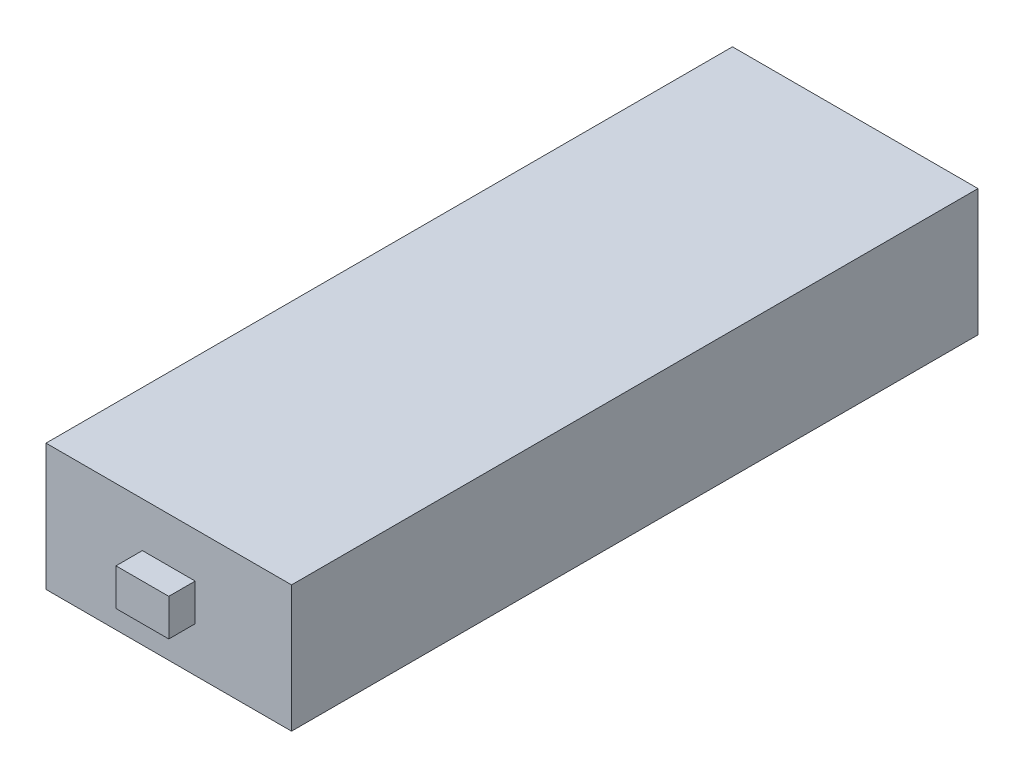
SolidWorks part; units mm, degrees
ref_plane "Front Plane" through (0, 0, 0) normal (0, 0, 1) x (1, 0, 0)
ref_plane "Top Plane" through (0, 0, 0) normal (0, 1, 0) x (1, 0, 0)
ref_plane "Right Plane" through (0, 0, 0) normal (1, 0, 0) x (0, 0, -1)
sketch "Sketch1" plane through (0, 0, 0) normal (0, 1, 0) x (1, 0, 0)
  line L1 (23.25, -65) -> (-23.25, -65)
  line L2 (23.25, -65) -> (23.25, 65)
  line L3 (23.25, 65) -> (-23.25, 65)
  line L4 (-23.25, -65) -> (-23.25, 65)
  line L5 (23.25, -65) -> (-23.25, 65) construction
  line L6 (23.25, 65) -> (-23.25, -65) construction
  point P0 (0, 0)
  dimension "D1" = 46.5
  dimension "D2" = 130
extrude "body" add sketch "Sketch1" along normal blind 24
sketch "Sketch2" plane through (0, 0, 65) normal (0, 0, 1) x (1, 0, 0)
  line L0 (-23.25, 24) -> (-23.25, 0) construction
  line L1 (5, 8.5) -> (-5, 8.5)
  line L2 (5, 8.5) -> (5, 15.5)
  line L3 (5, 15.5) -> (-5, 15.5)
  line L4 (-5, 8.5) -> (-5, 15.5)
  line L5 (5, 8.5) -> (-5, 15.5) construction
  line L6 (5, 15.5) -> (-5, 8.5) construction
  point P0 (0, 12)
  point P5 (0, 0)
  point P9 (-23.25, 12)
  dimension "D1" = 7
  dimension "D2" = 10
extrude "cables" add sketch "Sketch2" along normal blind 5
